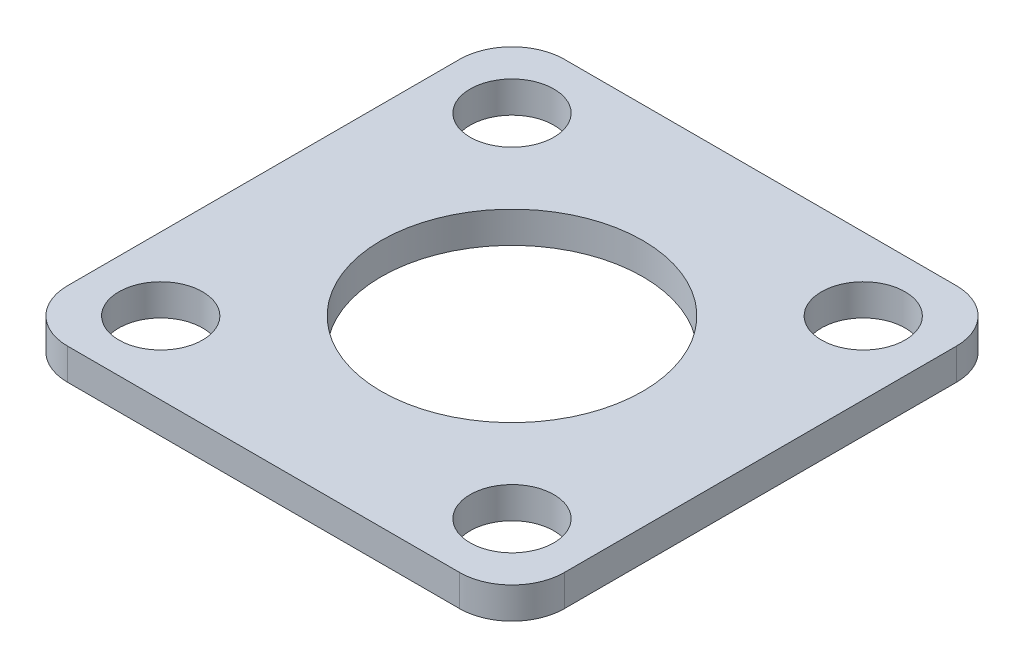
SolidWorks part; units mm, degrees
ref_plane "Front Plane" through (0, 0, 0) normal (0, 0, 1) x (1, 0, 0)
ref_plane "Top Plane" through (0, 0, 0) normal (0, 1, 0) x (1, 0, 0)
ref_plane "Right Plane" through (0, 0, 0) normal (1, 0, 0) x (0, 0, -1)
sketch "Sketch1" plane through (0, 0, 0) normal (0, 1, 0) x (1, 0, 0)
  line L1 (-9.5, 9.5) -> (9.5, 9.5)
  line L2 (-9.5, 9.5) -> (-9.5, -9.5)
  line L3 (-9.5, -9.5) -> (9.5, -9.5)
  line L4 (9.5, 9.5) -> (9.5, -9.5)
  circle A0 centre (0, 0) radius 5
  circle A1 centre (6.7175, -6.7175) radius 1.6
  circle A2 centre (-6.7175, -6.7175) radius 1.6
  circle A3 centre (-6.7175, 6.7175) radius 1.6
  circle A4 centre (6.7175, 6.7175) radius 1.6
  point P14 (0, 0)
  dimension "D1" = 10
  dimension "D3" = 3.2
  dimension "D2" = 9.5
  dimension "D5" = 9.5
  dimension "D6" = 9.5
  dimension "D7" = 9.5
  dimension "D8" = 9.5
  dimension "D4" = 4
extrude "Boss-Extrude1" add sketch "Sketch1" along normal blind 1.2
fillet "Fillet1" radius 2 4 edges at (-9.5, 0.6, -9.5) (9.5, 0.6, -9.5) (-9.5, 0.6, 9.5) (9.5, 0.6, 9.5)
